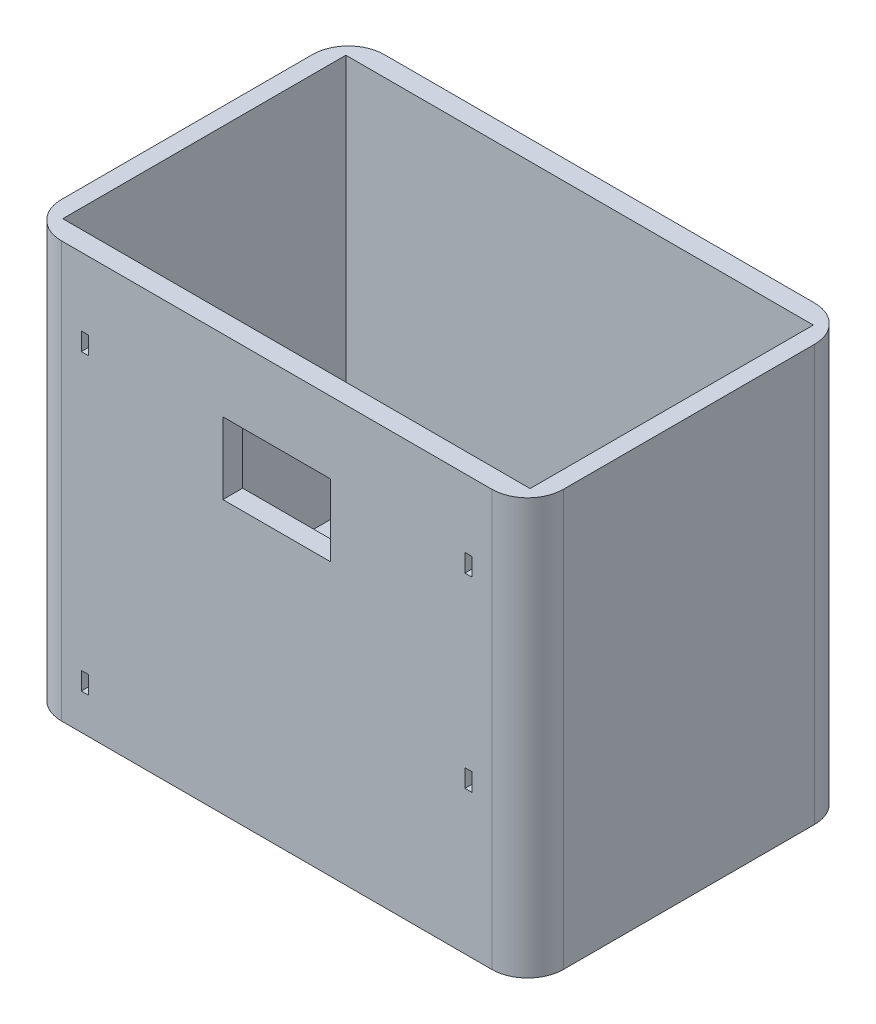
SolidWorks part; units mm, degrees
ref_plane "前视基准面" through (0, 0, 0) normal (0, 0, 1) x (1, 0, 0)
ref_plane "上视基准面" through (0, 0, 0) normal (0, 1, 0) x (1, 0, 0)
ref_plane "右视基准面" through (0, 0, 0) normal (1, 0, 0) x (0, 0, -1)
sketch "草图1" plane through (0, 0, 0) normal (0, 1, 0) x (1, 0, 0)
  line L1 (-35, 22.5) -> (35, 22.5)
  line L2 (-35, 22.5) -> (-35, -22.5)
  line L3 (-35, -22.5) -> (35, -22.5)
  line L4 (35, 22.5) -> (35, -22.5)
  line L5 (-35, 22.5) -> (35, -22.5) construction
  line L6 (-35, -22.5) -> (35, 22.5) construction
  point P0 (0, 0)
  dimension "D1" = 70
  dimension "D2" = 45
extrude "凸台-拉伸1" add sketch "草图1" along normal blind 3
ref_plane "基准面1" through (0, 3, 0) normal (0, 1, 0) x (1, 0, 0)
sketch "草图2" plane through (0, 3, 0) normal (0, 1, 0) x (1, 0, 0)
  line L0 (35, 22.5) -> (-35, 22.5) construction
  line L1 (17.5, 11.5) -> (30.5, 11.5)
  line L2 (17.5, 11.5) -> (17.5, -11.5)
  line L3 (17.5, -11.5) -> (30.5, -11.5)
  line L4 (30.5, 11.5) -> (30.5, -11.5)
  line L5 (35, -22.5) -> (35, 22.5) construction
  line L6 (-30.5, 11.5) -> (-17.5, 11.5)
  line L7 (-30.5, 11.5) -> (-30.5, -11.5)
  line L8 (-30.5, -11.5) -> (-17.5, -11.5)
  line L9 (-17.5, 11.5) -> (-17.5, -11.5)
  dimension "D1" = 23
  dimension "D2" = 13
  dimension "D3" = 11
  dimension "D4" = 11
  dimension "D5" = 23
  dimension "D6" = 13
  dimension "D7" = 35
  dimension "D8" = 4.5
extrude "切除-拉伸1" cut sketch "草图2" against normal blind 10
sketch "草图3" plane through (0, 3, 0) normal (0, 1, 0) x (1, 0, 0)
  line L0 (-24, 11.5) -> (-24, 14) construction
  line L1 (-17.5, 11.5) -> (-30.5, 11.5) construction
  line L2 (-24, -11.5) -> (-24, -14) construction
  line L3 (-30.5, -11.5) -> (-17.5, -11.5) construction
  line L4 (24, 11.5) -> (24, 14) construction
  line L5 (30.5, 11.5) -> (17.5, 11.5) construction
  line L6 (24, -11.5) -> (24, -14) construction
  line L7 (17.5, -11.5) -> (30.5, -11.5) construction
  circle A0 centre (-24, 14) radius 0.95
  circle A1 centre (-24, -14) radius 0.95
  circle A2 centre (24, 14) radius 0.95
  circle A3 centre (24, -14) radius 0.95
  dimension "D2" = 1.9
  dimension "D4" = 1.9
  dimension "D7" = 1.9
  dimension "D8" = 1.9
  dimension "D1" = 2.5
  dimension "D3" = 2.5
  dimension "D5" = 2.5
  dimension "D6" = 2.5
extrude "切除-拉伸2" cut sketch "草图3" against normal blind 10
fillet "圆角1" radius 5 1 edges at (35, 1.5, -22.5)
fillet "圆角2" radius 5 3 edges at (-35, 1.5, -22.5) (-35, 1.5, 22.5) (35, 1.5, 22.5)
sketch "草图4" plane through (0, 3, 0) normal (0, 1, 0) x (1, 0, 0)
  circle A0 centre (-30, 17.5) radius 0.95
  circle A1 centre (30, 17.5) radius 0.95
  circle A2 centre (-30, -17.5) radius 0.95
  circle A3 centre (30, -17.5) radius 0.95
  dimension "D1" = 1.9
  dimension "D2" = 1.9
  dimension "D3" = 1.9
  dimension "D4" = 1.9
extrude "切除-拉伸3" cut sketch "草图4" against normal blind 10
sketch "草图8" plane through (0, 3, 0) normal (0, 1, 0) x (1, 0, 0)
  line L0 (-27, 17.5) -> (27, 17.5)
  line L2 (30, 14.5) -> (30, -14.5)
  line L3 (-27, -17.5) -> (27, -17.5)
  line L4 (-30, 14.5) -> (-30, -14.5)
  arc A0 (-30, 14.5) -> (-27, 17.5) centre (-30, 17.5) ccw
  arc A1 (27, 17.5) -> (30, 14.5) centre (30, 17.5) ccw
  arc A2 (-27, -17.5) -> (-30, -14.5) centre (-30, -17.5) ccw
  arc A3 (30, -14.5) -> (27, -17.5) centre (30, -17.5) ccw
  dimension "D1" = 6
  dimension "D2" = 6
  dimension "D3" = 6
  dimension "D4" = 6
extrude "切除-拉伸4" cut sketch "草图8" against normal blind 10
sketch "草图9" plane through (0, 3, 0) normal (0, 1, 0) x (1, 0, 0)
  line L1 (-32.5913, 19.7445) -> (32.5913, 19.7445)
  line L2 (-32.5913, 19.7445) -> (-32.5913, -19.7445)
  line L3 (-32.5913, -19.7445) -> (32.5913, -19.7445)
  line L4 (32.5913, 19.7445) -> (32.5913, -19.7445)
  line L5 (-32.5913, 19.7445) -> (32.5913, -19.7445) construction
  line L6 (-32.5913, -19.7445) -> (32.5913, 19.7445) construction
  line L7 (-30, -22.5) -> (30, -22.5)
  line L8 (-35, -17.5) -> (-35, 17.5)
  line L9 (-30, 22.5) -> (30, 22.5)
  line L10 (35, -17.5) -> (35, 17.5)
  line L11 (-35, -22.5) -> (35, 22.5) construction
  line L12 (-35, 22.5) -> (35, -22.5) construction
  arc A0 (35, -17.5) -> (30, -22.5) centre (30, -17.5) cw
  arc A1 (-30, -22.5) -> (-35, -17.5) centre (-30, -17.5) cw
  arc A2 (35, 17.5) -> (30, 22.5) centre (30, 17.5) ccw
  arc A3 (-35, 17.5) -> (-30, 22.5) centre (-30, 17.5) cw
  point P0 (0, 0)
  point P6 (0, 0)
  dimension "D1" = 45
  dimension "D2" = 70
  dimension "D3" = 5
extrude "凸台-拉伸2" add sketch "草图9" along normal blind 55
ref_plane "基准面2" through (0, 0, 22.5) normal (0, 0, 1) x (1, 0, 0)
ref_plane "基准面3" through (0, 0, 22.5) normal (0, 0, -1) x (-1, 0, 0)
sketch "草图10" plane through (0, 0, 22.5) normal (0, 0, -1) x (-1, 0, 0)
  line L0 (0, 58) -> (0, 0) construction
  line L1 (30, 58) -> (-30, 58) construction
  line L2 (21.7189, 3) -> (-21.7189, 3) construction
  line L3 (27.25, 7.5) -> (26.25, 7.5)
  line L4 (27.25, 7.5) -> (27.25, 5)
  line L5 (27.25, 5) -> (26.25, 5)
  line L6 (26.25, 7.5) -> (26.25, 5)
  line L7 (27.25, 7.5) -> (26.25, 5) construction
  line L8 (27.25, 5) -> (26.25, 7.5) construction
  line L9 (27.25, 48.5) -> (26.25, 48.5)
  line L10 (-26.25, 22.5) -> (-27.25, 22.5)
  line L11 (-26.25, 22.5) -> (-26.25, 20)
  line L12 (-26.25, 20) -> (-27.25, 20)
  line L13 (-27.25, 22.5) -> (-27.25, 20)
  line L14 (-26.25, 22.5) -> (-27.25, 20) construction
  line L15 (-26.25, 20) -> (-27.25, 22.5) construction
  line L16 (-27.25, 48.5) -> (-26.25, 48.5)
  line L17 (-27.25, 48.5) -> (-27.25, 46)
  line L18 (-27.25, 46) -> (-26.25, 46)
  line L19 (-26.25, 48.5) -> (-26.25, 46)
  line L20 (-27.25, 48.5) -> (-26.25, 46) construction
  line L21 (-27.25, 46) -> (-26.25, 48.5) construction
  line L22 (26.25, 48.5) -> (26.25, 46)
  line L23 (27.25, 46) -> (26.25, 46)
  line L24 (27.25, 48.5) -> (27.25, 46)
  line L26 (7.5, 48) -> (-7.5, 48)
  line L27 (7.5, 48) -> (7.5, 38)
  line L28 (7.5, 38) -> (-7.5, 38)
  line L29 (-7.5, 48) -> (-7.5, 38)
  line L30 (7.5, 48) -> (-7.5, 38) construction
  line L31 (7.5, 38) -> (-7.5, 48) construction
  point P5 (26.75, 6.25)
  point P12 (-26.75, 21.25)
  point P17 (-26.75, 47.25)
  point P26 (0, 43)
  dimension "D1" = 1
  dimension "D2" = 2.5
  dimension "D3" = 26.25
  dimension "D4" = 2
  dimension "D5" = 1
  dimension "D6" = 2.5
  dimension "D7" = 17
  dimension "D8" = 26.25
  dimension "D9" = 1
  dimension "D10" = 2.5
  dimension "D11" = 0
  dimension "D12" = 23.5
  dimension "D13" = 15
  dimension "D14" = 10
  dimension "D15" = 10
extrude "切除-拉伸5" cut sketch "草图10" along normal blind 7
